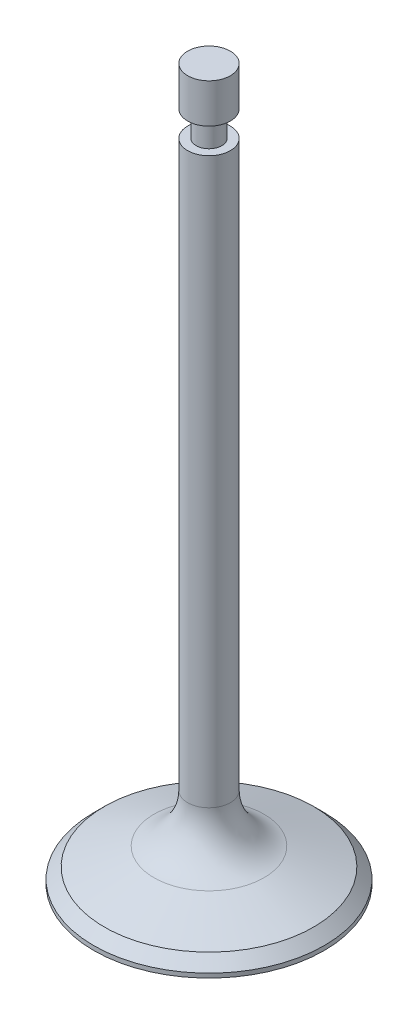
SolidWorks part; units mm, degrees
ref_plane "Front Plane" through (0, 0, 0) normal (0, 0, 1) x (1, 0, 0)
ref_plane "Top Plane" through (0, 0, 0) normal (0, 1, 0) x (1, 0, 0)
ref_plane "Right Plane" through (0, 0, 0) normal (1, 0, 0) x (0, 0, -1)
sketch "Sketch1" plane through (0, 0, 0) normal (0, 0, 1) x (1, 0, 0)
  line L10 (0, 0) -> (0, 84.495)
  line L11 (0, 84.495) -> (2.5, 84.495)
  line L12 (2.5, 84.495) -> (2.5, 79.895)
  line L13 (2.5, 79.895) -> (1.5, 79.895)
  line L14 (1.5, 79.895) -> (1.5, 76.895)
  line L15 (1.5, 76.895) -> (2.5, 76.895)
  line L16 (2.5, 76.895) -> (2.5, 10.75)
  line L17 (6.4479, 5.1118) -> (12.25, 3)
  line L18 (12.25, 3) -> (13.5, 1.75)
  line L19 (13.5, 1.75) -> (13.5, 1.25)
  line L20 (12.25, 3) -> (4.3779, 3) construction
  line L21 (0, 0) -> (-9.47, 0) construction
  arc A2 (2.5, 10.75) -> (6.4479, 5.1118) centre (8.5, 10.75) ccw
  arc A3 (13.5, 1.25) -> (0, 0) centre (0, 73.525) cw
  dimension "D7" = 6
  dimension "D1" = 84.495
  dimension "D2" = 2.5
  dimension "D3" = 4.6
  dimension "D4" = 1
  dimension "D5" = 3
  dimension "D6" = 20
  dimension "D8" = 45
  dimension "D9" = 1.25
  dimension "D10" = 0.5
  dimension "D11" = 13.5
  dimension "D12" = 1.25
revolve "Revolve1" add sketch "Sketch1" angle 360 about L10
